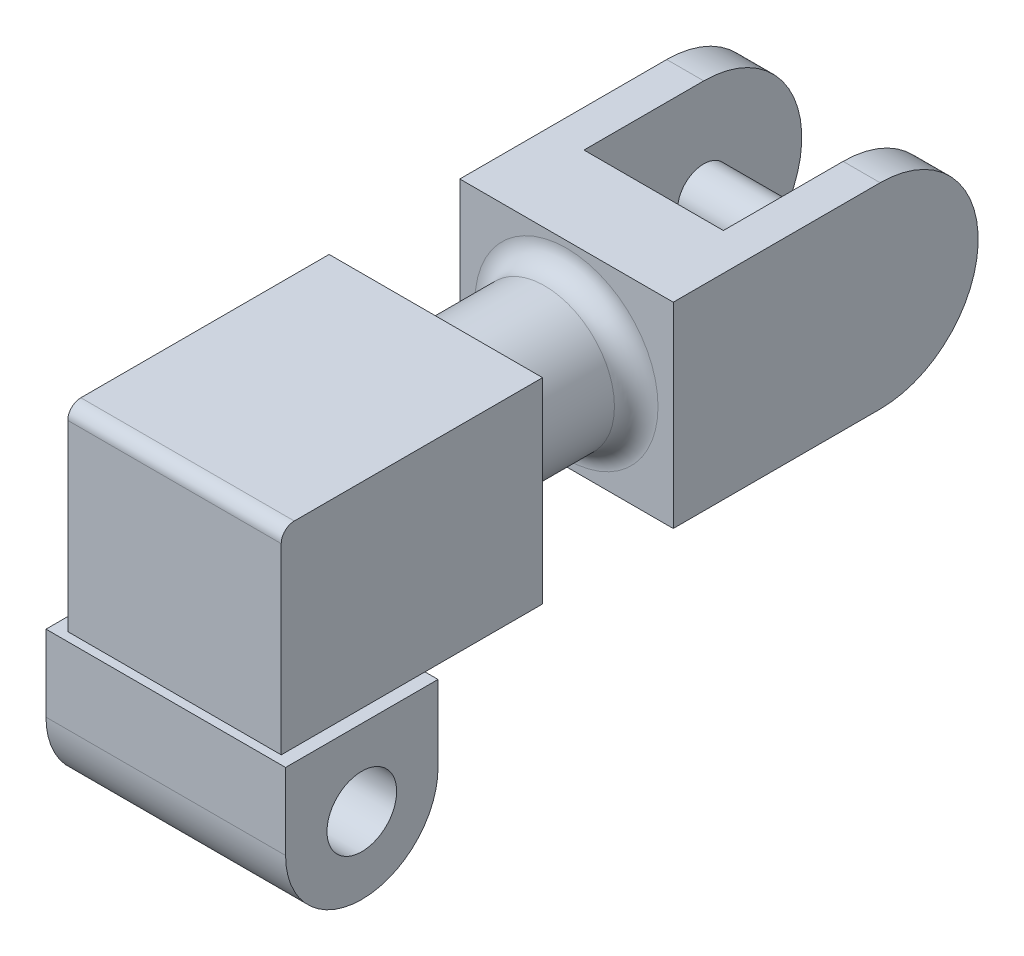
SolidWorks part; units mm, degrees
ref_plane "Front Plane" through (0, 0, 0) normal (0, 0, 1) x (1, 0, 0)
ref_plane "Top Plane" through (0, 0, 0) normal (0, 1, 0) x (1, 0, 0)
ref_plane "Right Plane" through (0, 0, 0) normal (1, 0, 0) x (0, 0, -1)
sketch "Sketch1" plane through (0, 0, 0) normal (1, 0, 0) x (0, 0, -1)
  line L0 (-17.5, 0) -> (-17.5, 17.5)
  line L1 (-17.5, 17.5) -> (17.5, 17.5)
  line L2 (17.5, 17.5) -> (17.5, 0)
  arc A0 (-17.5, 0) -> (17.5, 0) centre (0, 0) ccw
  circle A1 centre (0, 0) radius 8
  dimension "D3" = 17.5
extrude "Boss-Extrude1" add sketch "Sketch1" along normal mid plane 55
sketch "Sketch2" plane through (0, 17.5, 0) normal (0, 1, 0) x (1, 0, 0)
  line L0 (-24.5, -15.5) -> (24.5, -15.5)
  line L2 (-24.5, -15.5) -> (-24.5, 44.5)
  line L3 (-24.5, 44.5) -> (24.5, 44.5)
  line L4 (24.5, -15.5) -> (24.5, 44.5)
  point P0 (0, 0)
  dimension "D1" = 49
  dimension "D2" = 2
  dimension "D3" = 60
extrude "Boss-Extrude2" add sketch "Sketch2" along normal blind 45
sketch "Sketch3" plane through (0, 0, -44.5) normal (0, 0, -1) x (-1, 0, 0)
  circle A0 centre (0, 40) radius 16
  dimension "D1" = 32
extrude "Boss-Extrude3" add sketch "Sketch3" along normal blind 30
sketch "Sketch4" plane through (0, 0, -74.5) normal (0, 0, -1) x (-1, 0, 0)
  line L1 (-24.5, 17.5) -> (24.5, 17.5)
  line L2 (-24.5, 17.5) -> (-24.5, 62.5)
  line L3 (-24.5, 62.5) -> (24.5, 62.5)
  line L4 (24.5, 17.5) -> (24.5, 62.5)
  line L5 (-24.5, 17.5) -> (24.5, 62.5) construction
  line L6 (-24.5, 62.5) -> (24.5, 17.5) construction
  point P0 (0, 40)
extrude "Boss-Extrude4" add sketch "Sketch4" along normal blind 47.5
sketch "Sketch5" plane through (24.5, 0, 0) normal (1, 0, 0) x (0, 0, -1)
  line L0 (122, 62.5) -> (122, 17.5) construction
  line L1 (122, 62.5) -> (122, 17.5)
  arc A0 (122, 17.5) -> (122, 62.5) centre (122, 40) ccw
extrude "Boss-Extrude5" add sketch "Sketch5" against normal blind 49
sketch "Sketch6" plane through (0, 62.5, 0) normal (0, 1, 0) x (1, 0, 0)
  line L0 (-12.3971, 94.5) -> (12.3971, 94.5)
  line L5 (-12.3971, 94.5) -> (-12.3971, 144.5)
  line L6 (24.5, 144.5) -> (-24.5, 144.5) construction
  line L7 (-12.3971, 144.5) -> (12.3971, 144.5)
  line L8 (12.3971, 144.5) -> (12.3971, 94.5)
  point P0 (0, 98.113)
  dimension "D1" = 20
extrude "Cut-Extrude1" cut sketch "Sketch6" against normal through all
sketch "Sketch7" plane through (24.5, 0, 0) normal (1, 0, 0) x (0, 0, -1)
  circle A0 centre (122, 40) radius 6
  dimension "D1" = 12
extrude "Cut-Extrude2" cut sketch "Sketch7" against normal through all
sketch "Sketch8" plane through (24.5, 0, 0) normal (1, 0, 0) x (0, 0, -1)
  circle A0 centre (122, 40) radius 6 construction
  circle A1 centre (122, 40) radius 6
extrude "Boss-Extrude6" add sketch "Sketch8" against normal blind 49
fillet "Fillet1" radius 5 1 edges at (-16, 40, -44.5)
fillet "Fillet2" radius 5 1 edges at (-16, 40, -74.5)
fillet "Fillet4" radius 3 1 edges at (0, 62.5, 15.5)
sketch "Sketch9" plane through (0, 62.5, 0) normal (0, 1, 0) x (1, 0, 0)
  line L0 (-21, 74.5) -> (21, 74.5) construction
  line L1 (-12.3971, 94.5) -> (12.3971, 94.5) construction
  line L2 (-21, 74.5) -> (21, 74.5)
  line L3 (-12.3971, 94.5) -> (12.3971, 94.5)
  line L4 (24.5, 144.5) -> (12.3971, 144.5) construction
  line L6 (-16, 97.6852) -> (-16, 144.5)
  line L7 (-16, 144.5) -> (16, 144.5)
  line L8 (16, 94.5) -> (16, 144.5)
  line L9 (16, 94.5) -> (-16, 94.5)
  line L10 (-16, 94.5) -> (-16, 97.6852)
  point P4 (0, 121.0926)
  dimension "D1" = 32
  dimension "D2" = 50
sketch "Sketch10" plane through (0, 62.5, 0) normal (0, 1, 0) x (1, 0, 0)
  line L0 (16, 94.5) -> (16, 144.5) construction
  line L1 (16, 94.5) -> (-16, 94.5) construction
  line L2 (-16, 94.5) -> (-16, 97.6852) construction
  line L3 (-16, 97.6852) -> (-16, 144.5) construction
  line L4 (-16, 144.5) -> (16, 144.5) construction
  line L5 (16, 94.5) -> (16, 144.5)
  line L6 (16, 94.5) -> (-16, 94.5)
  line L7 (-16, 94.5) -> (-16, 97.6852)
  line L8 (-16, 97.6852) -> (-16, 144.5)
  line L9 (-16, 144.5) -> (16, 144.5)
extrude "Cut-Extrude4" cut sketch "Sketch10" against normal through all
sketch "Sketch11" plane through (16, 0, 0) normal (-1, 0, 0) x (0, 0, 1)
  circle A0 centre (-122, 40) radius 6
  dimension "D1" = 12
sketch "Sketch12" plane through (16, 0, 0) normal (-1, 0, 0) x (0, 0, 1)
  circle A0 centre (-122, 40) radius 6 construction
  circle A1 centre (-122, 40) radius 6
extrude "Boss-Extrude7" add sketch "Sketch12" along normal up to surface (32 mm away) up to face at (-16, 40, -113.875)
sketch "Sketch13" plane through (0, 0, 0) normal (1, 0, 0) x (0, 0, -1)
  point P0 (122, 40)
